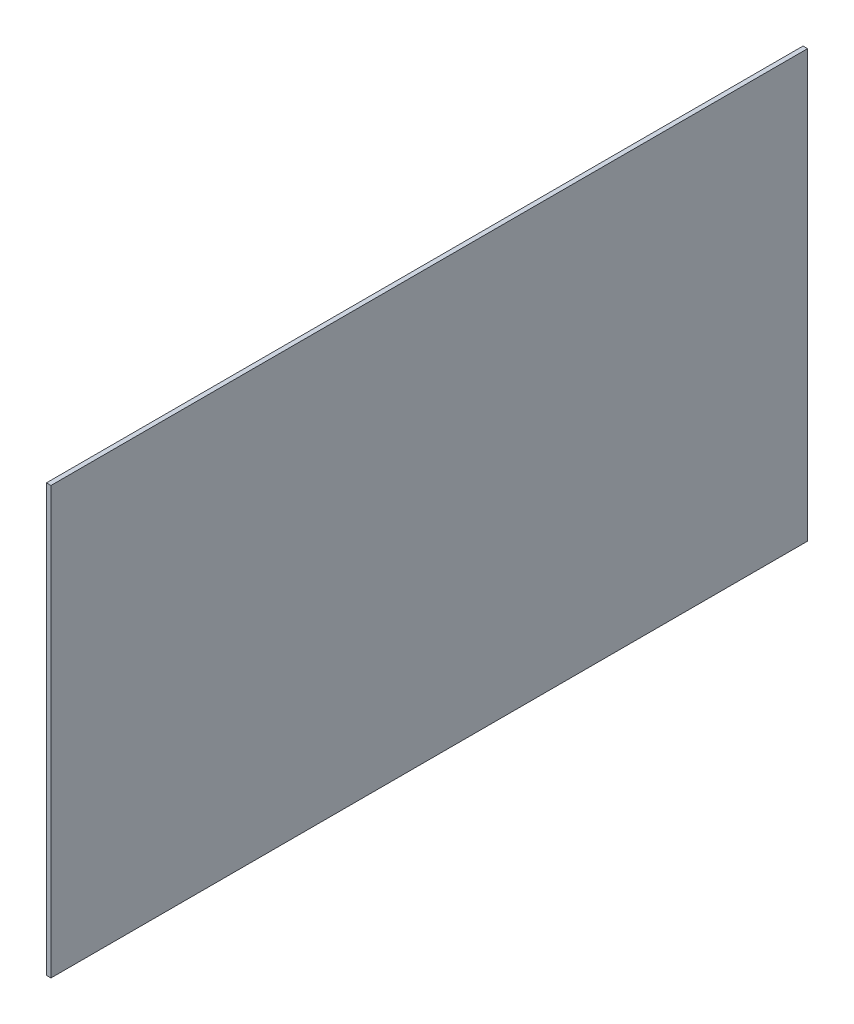
SolidWorks part; units mm, degrees
ref_plane "Front Plane" through (0, 0, 0) normal (0, 0, 1) x (1, 0, 0)
ref_plane "Top Plane" through (0, 0, 0) normal (0, 1, 0) x (1, 0, 0)
ref_plane "Right Plane" through (0, 0, 0) normal (1, 0, 0) x (0, 0, -1)
sketch "Sketch1" plane through (0, 0, 0) normal (1, 0, 0) x (0, 0, -1)
  line L0 (-250, 140.9304) -> (-250, -140.9304)
  line L1 (250, -140.9304) -> (250, 140.9304)
  line L2 (-250, 140.9304) -> (250, 140.9304)
  line L3 (-250, -140.9304) -> (250, -140.9304)
extrude "Boss-Extrude1" add sketch "Sketch1" along normal blind 3
